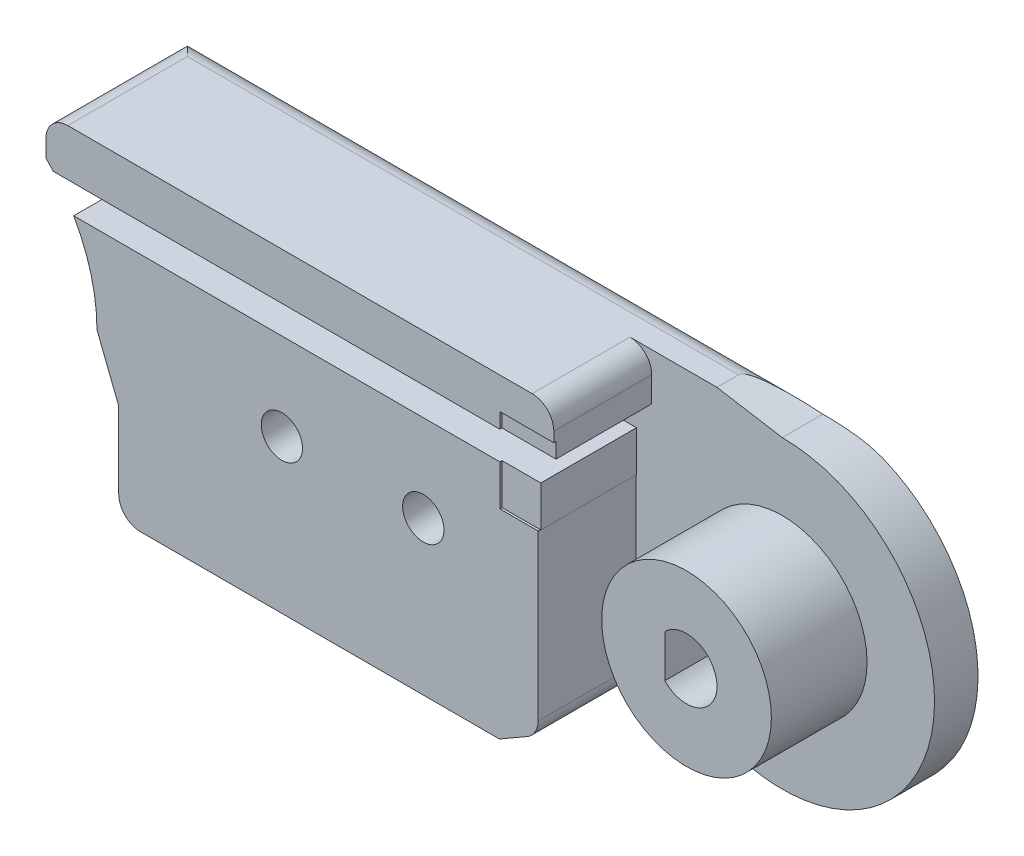
SolidWorks part; units mm, degrees
ref_plane "Front Plane" through (0, 0, 0) normal (0, 0, 1) x (1, 0, 0)
ref_plane "Top Plane" through (0, 0, 0) normal (0, 1, 0) x (1, 0, 0)
ref_plane "Right Plane" through (0, 0, 0) normal (1, 0, 0) x (0, 0, -1)
sketch "Sketch3" plane through (0, 0, 0) normal (0, 0, 1) x (1, 0, 0)
  line L7 (8, 0) -> (9, -2.5431)
  line L11 (35, 6.9569) -> (32, 7.4569)
  line L18 (5.6569, 5.6569) -> (5.6569, 7.4569)
  line L19 (5.6569, 7.4569) -> (32, 7.4569)
  line L20 (26.5, -7.0431) -> (9, -7.0431)
  line L21 (9, -7.0431) -> (9, -2.5431)
  line L23 (30.0502, -4.9929) -> (26.5, -7.0431)
  arc A4 (8, 0) -> (5.6569, 5.6569) centre (0, 0) ccw
  arc A5 (30.0502, -4.9929) -> (35, 6.9569) centre (35, -0.0431) ccw
  dimension "D3" = 3.5503
  dimension "D10" = 2.5431
  dimension "D17" = 14
  dimension "D4" = 5.6569
  dimension "D5" = 135
  dimension "D2" = 35
  dimension "D6" = 14.5
  dimension "D7" = 4.5
  dimension "D8" = 1
  dimension "D9" = 45
  dimension "D11" = 1.8
  dimension "D14" = 3
extrude "Boss-Extrude1" add sketch "Sketch3" along normal blind 2 contours A5 L11 L19 L18 A4 L7 L21 L20 L23
sketch "Sketch20" plane through (0, 0, 0) normal (0, 0, 1) x (1, 0, 0)
  line L0 (0, 7) -> (0, 7.5) construction
  line L1 (0, 7.5) -> (-19.4737, 7.5) construction
  line L2 (0, 5.3) -> (-14, 5.3) construction
  line L3 (0, 4) -> (-14, 4) construction
  line L4 (-14, 4) -> (-14, 5.3) construction
  line L5 (0, 5.3) -> (17.4849, 5.3) construction
  line L6 (17.4849, 5.3) -> (17.4849, 4) construction
  line L7 (17.4849, 4) -> (0, 4) construction
  line L8 (-2.5, 7.5) -> (-2.5, 2.868) construction
  circle A0 centre (0, 0) radius 7 construction
  circle A1 centre (0, 0) radius 3.9 construction
  circle A3 centre (0, 0) radius 5.3 construction
  circle A4 centre (0, 0) radius 4 construction
  circle A5 centre (0, 0) radius 2 construction
  dimension "D1" = 0
  dimension "D2" = 2.5
ref_plane "Plane1" through (0, 0, 2) normal (0, 0, 1) x (1, 0, 0)
sketch "Sketch4" plane through (0, 0, 2) normal (0, 0, 1) x (1, 0, 0)
  line L4 (5.6569, 5.6569) -> (5.6569, 7.5)
  line L5 (5.6569, 5.6569) -> (5.6569, 7.4569) construction
  line L6 (5.6569, 7.5) -> (26.5, 7.5)
  line L10 (8, 0) -> (9, -2.5431)
  line L11 (9, -2.5431) -> (9, -7.0431)
  line L12 (9, -7.0431) -> (26.5, -7.0431)
  line L13 (26.5, -7.0431) -> (26.5, 7.5)
  arc A0 (8, 0) -> (5.6569, 5.6569) centre (0, 0) ccw construction
  arc A3 (8, 0) -> (5.6569, 5.6569) centre (0, 0) ccw
sketch "Sketch22" plane through (0, 0, 2) normal (0, 0, 1) x (1, 0, 0)
  line L1 (5.6569, 7.4569) -> (26.5, 7.4569)
  line L6 (8, 0) -> (9, -2.5431)
  line L7 (9, -2.5431) -> (9, -7.0431)
  line L8 (9, -7.0431) -> (26.5, -7.0431)
  line L10 (26.5, 7.4569) -> (32, 7.4569)
  line L11 (32, 7.4569) -> (32, 2.1289)
  line L12 (32, 2.1289) -> (28.2751, 2.1289)
  line L13 (26.5, -7.0431) -> (28.2751, -6.018)
  line L14 (30.0502, -4.9929) -> (26.5, -7.0431) construction
  line L15 (28.2751, -6.018) -> (28.2751, 2.1289)
  line L16 (5.6569, 7.4569) -> (5.6569, 5.6569)
  arc A0 (8, 0) -> (5.6569, 5.6569) centre (0, 0) ccw
  dimension "D1" = 5.328
extrude "Boss-Extrude6" add sketch "Sketch22" along normal blind 4.5
sketch "Sketch25" plane through (0, 0, 2) normal (0, 0, 1) x (1, 0, 0)
  line L0 (0, 5.3) -> (18.0981, 5.3) construction
  line L1 (0, 4) -> (18.0981, 4) construction
  line L2 (18.0981, 4) -> (18.0981, 5.3) construction
sketch "Sketch26" plane through (0, 0, 2) normal (0, 0, 1) x (1, 0, 0)
  line L1 (18.0981, 5.3) -> (2.5301, 5.3)
  line L2 (18.0981, 4) -> (2.5301, 4)
  line L3 (2.5301, 5.3) -> (2.5301, 4)
  line L4 (18.0981, 5.3) -> (32, 5.3)
  line L5 (32, 2.1289) -> (32, 7.4569) construction
  line L6 (32, 5.3) -> (32, 4)
  line L7 (32, 4) -> (18.0981, 4)
extrude "Cut-Extrude6" cut sketch "Sketch26" along normal blind 4.5
ref_plane "Plane18" through (0, 0, 6.5) normal (0, 0, 1) x (1, 0, 0)
sketch "Sketch31" plane through (0, 0, 6.5) normal (0, 0, 1) x (1, 0, 0)
  line L0 (2.4327, 5.6569) -> (0, 5.6569)
  line L4 (9, -5.6569) -> (0, -5.6569)
  line L7 (2.4327, 5.6569) -> (5.6569, 5.6569)
  line L8 (5.6569, 5.6569) -> (5.6569, 7.4569)
  line L12 (9, -7.0431) -> (9, -5.6569)
  line L13 (9, -2.5431) -> (9, -7.0431) construction
  line L16 (32, 7.4569) -> (32, 2.1289)
  line L17 (32, 2.1289) -> (28.2751, 2.1289)
  line L22 (5.6569, 7.4569) -> (5.6569, 8.9569)
  line L23 (5.6569, 8.9569) -> (32, 8.9569)
  line L24 (32, 8.9569) -> (32, 7.4569)
  line L25 (9, -7.0431) -> (9, -8.5431)
  line L26 (9, -8.5431) -> (26.5, -8.5431)
  line L27 (26.5, -8.5431) -> (26.5, -7.0431)
  line L28 (26.5, -7.0431) -> (26.5, 2.1289)
  line L29 (26.5, 2.1289) -> (28.2751, 2.1289)
  line L30 (9, -7.0431) -> (26.5, -7.0431) construction
  line L31 (32, 7.4569) -> (5.6569, 7.4569) construction
  arc A0 (0, 5.6569) -> (0, -5.6569) centre (0, 0) ccw
  dimension "D1" = 5.6569
  dimension "D2" = 5.6569
  dimension "D3" = 1.5
  dimension "D4" = 1.5
extrude "Boss-Extrude14" add sketch "Sketch31" along normal blind 2.3 separate body
sketch "Sketch32" plane through (0, 0, 8.8) normal (0, 0, 1) x (1, 0, 0)
  circle A0 centre (0, 0) radius 3
  dimension "D1" = 6
extrude "Cut-Extrude7" cut sketch "Sketch32" against normal blind 2.3
sketch "Sketch33" plane through (0, 0, 8.8) normal (0, 0, 1) x (1, 0, 0)
  line L1 (5.6569, 8.9569) -> (5.6569, 6.9569)
  line L4 (9, -7.0431) -> (9, -8.5431)
  line L7 (7, -4.1569) -> (25.5, -4.1569)
  line L11 (9, -8.5431) -> (26.5, -8.5431)
  line L15 (26.5, -8.5431) -> (26.5, -7.0431)
  line L16 (26.5, -7.0431) -> (9, -7.0431)
  line L17 (5.6569, 8.9569) -> (28, 8.9569)
  line L18 (32, 8.9569) -> (5.6569, 8.9569) construction
  line L21 (28, 6.9569) -> (28, 8.9569)
  line L22 (25.5, -4.1569) -> (25.5, -2.1569)
  line L23 (25.5, -2.1569) -> (7, -2.1569)
  line L27 (5.6569, 6.9569) -> (28, 6.9569)
  line L28 (25.5, 2.172) -> (7, 2.172)
  line L30 (7, 4.172) -> (25.5, 4.172)
  line L33 (25.5, 2.172) -> (25.5, 4.172)
  line L34 (32, 2.1289) -> (32, 8.9569) construction
  line L35 (9, -8.5431) -> (26.5, -8.5431) construction
  line L37 (26.5, -8.5431) -> (26.5, 2.1289) construction
  arc A1 (7, -2.1569) -> (7, -4.1569) centre (7, -3.1569) ccw
  arc A2 (7, 4.172) -> (7, 2.172) centre (7, 3.172) ccw
  dimension "D1" = 1.5
  dimension "D2" = 2
  dimension "D3" = 2
  dimension "D5" = 2
  dimension "D6" = 2.5
  dimension "D8" = 4
extrude "Boss-Extrude15" add sketch "Sketch33" along normal blind 1.2
sketch "Sketch34" plane through (0, 0, 2) normal (0, 0, 1) x (1, 0, 0)
  line L0 (35, 5.3) -> (18.0981, 5.3) construction
  line L1 (35, 4) -> (18.0981, 4) construction
  circle A0 centre (35, -0.0431) radius 2 construction
  circle A1 centre (35, -0.0431) radius 5.3431 construction
  circle A2 centre (35, -0.0431) radius 4.0431 construction
sketch "Sketch35" plane through (0, 0, 8.8) normal (0, 0, 1) x (1, 0, 0)
  line L0 (32, 2.1289) -> (32, 6)
  line L1 (32, 2.1289) -> (26.5203, 2.1289)
  line L2 (32, 6) -> (26.5203, 6)
  line L3 (26.5203, 2.1289) -> (26.5203, 6)
  line L4 (32, 2.1289) -> (32, 8.9569) construction
  dimension "D1" = 5.4796
extrude "Cut-Extrude8" cut sketch "Sketch35" against normal blind 2.4
sketch "Sketch36" plane through (0, 0, 6.4) normal (0, 0, 1) x (1, 0, 0)
  line L0 (32, 2.1289) -> (32, 4)
  line L1 (32, 2.1289) -> (28.3, 2.1289)
  line L2 (32, 4) -> (28.3, 4)
  line L3 (28.3, 2.1289) -> (28.3, 4)
  line L4 (26.5, -7.0431) -> (26.5, 7.5) construction
  dimension "D1" = 1.8
extrude "Cut-Extrude9" cut sketch "Sketch36" against normal blind 4.4
sketch "Sketch37" plane through (0, 0, 2) normal (0, 0, 1) x (1, 0, 0)
  circle A0 centre (35, -0.0431) radius 3.9
  dimension "D1" = 7.8
extrude "Boss-Extrude16" add sketch "Sketch37" along normal blind 4.4
sketch "Sketch39" plane through (0, 0, 6.4) normal (0, 0, 1) x (1, 0, 0)
  line L0 (34, 0.9367) -> (34, -1.0229)
  arc A0 (34, -1.0229) -> (34, 0.9367) centre (35, -0.0431) ccw
  dimension "D2" = 2.8
  dimension "D1" = 1
extrude "Cut-Extrude10" cut sketch "Sketch39" against normal through all
sketch "Sketch43" plane through (0, 0, 8.8) normal (0, 0, 1) x (1, 0, 0)
  line L2 (0, -5.6569) -> (9, -5.6569) construction
  circle A0 centre (16.5, 0) radius 2.5
  circle A1 centre (23, 0) radius 2.5
  dimension "D1" = 7.5
  dimension "D3" = 5
  dimension "D4" = 6.5
  dimension "D2" = 5.6569
extrude "Boss-Extrude17" add sketch "Sketch43" along normal blind 1.2
sketch "Sketch44" plane through (0, 0, 10) normal (0, 0, 1) x (1, 0, 0)
  circle A0 centre (16.5, 0) radius 0.95
  circle A1 centre (23, 0) radius 0.95
  dimension "D1" = 1.9
  dimension "D2" = 1.9
extrude "Cut-Extrude11" cut sketch "Sketch44" against normal through all
sketch "Sketch45" plane through (0, 0, 0) normal (0, 0, -1) x (-1, 0, 0)
  circle A0 centre (-16.5, 0) radius 2
  circle A1 centre (-23, 0) radius 2
extrude "Cut-Extrude12" cut sketch "Sketch45" against normal blind 4.5
ref_plane "Plane17" through (0, 0, 10) normal (0, 0, 1) x (1, 0, 0)
sketch "Sketch48" plane through (0, 0, 2) normal (0, 0, 1) x (1, 0, 0)
  circle A0 centre (35, -0.0431) radius 6 construction
  dimension "D1" = 12
sketch "Sketch49" plane through (0, 6.9569, 0) normal (0, -1, 0) x (1, 0, 0)
  line L0 (5.6569, 10) -> (28, 10) construction
  line L1 (28, 10) -> (28, 8.8) construction
  line L2 (5.6569, 10) -> (5.6569, 8.8) construction
  circle A0 centre (25, 10) radius 0.75
  dimension "D1" = 3
  dimension "D3" = 1.5
  dimension "D2" = 19.3431
sketch "Sketch50" plane through (0, 0, 10) normal (0, 0, 1) x (1, 0, 0)
  line L0 (25, 6.9569) -> (27.3935, -5.0795) construction
extrude "Cut-Extrude13" cut sketch "Sketch49" against normal blind 3
sketch "Sketch51" plane through (0, 0, 8.8) normal (0, 0, 1) x (1, 0, 0)
  line L0 (32, 8.9569) -> (29, 8.9569)
  line L1 (32, 8.9569) -> (32, 4.9913)
  line L2 (29, 8.9569) -> (29, 4.9913)
  line L3 (32, 4.9913) -> (29, 4.9913)
  line L5 (32, 8.9569) -> (28, 8.9569) construction
  line L7 (32, 6) -> (32, 8.9569) construction
  dimension "D1" = 3
extrude "Cut-Extrude14" cut sketch "Sketch51" against normal blind 6.8
fillet "Fillet1" radius 1.5 2 edges at (17.3284, 8.9569, 6.5) (17.75, -8.5431, 6.5)
fillet "Fillet3" radius 1 6 edges at (28.2751, -6.018, 4.25) (29, 7.4569, 4.25) (9, -7.0431, 3.25) (5.6569, 7.4569, 3.25) (17.75, -7.0431, 0) (18.8284, 7.4569, 0)
split "Split1" trim tools "Plane18" bodies to split 141 139 resulting bodies 143 144
delete or keep bodies "Body-Delete/Keep 1" type delete bodies bodies 143
